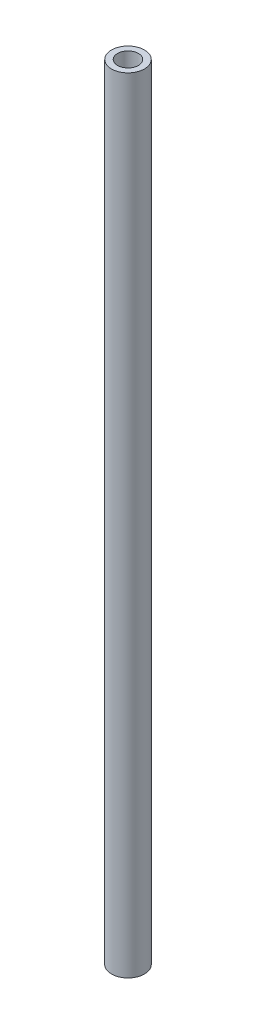
SolidWorks part; units mm, degrees
ref_plane "前视基准面" through (0, 0, 0) normal (0, 0, 1) x (1, 0, 0)
ref_plane "上视基准面" through (0, 0, 0) normal (0, 1, 0) x (1, 0, 0)
ref_plane "右视基准面" through (0, 0, 0) normal (1, 0, 0) x (0, 0, -1)
sketch "草图1" plane through (0, 0, 0) normal (0, 1, 0) x (1, 0, 0)
  circle A0 centre (0, 0) radius 2
  circle A1 centre (0, 0) radius 3.15
  dimension "D1" = 4
  dimension "D2" = 6.3
extrude "凸台-拉伸1" add sketch "草图1" along normal blind 150
